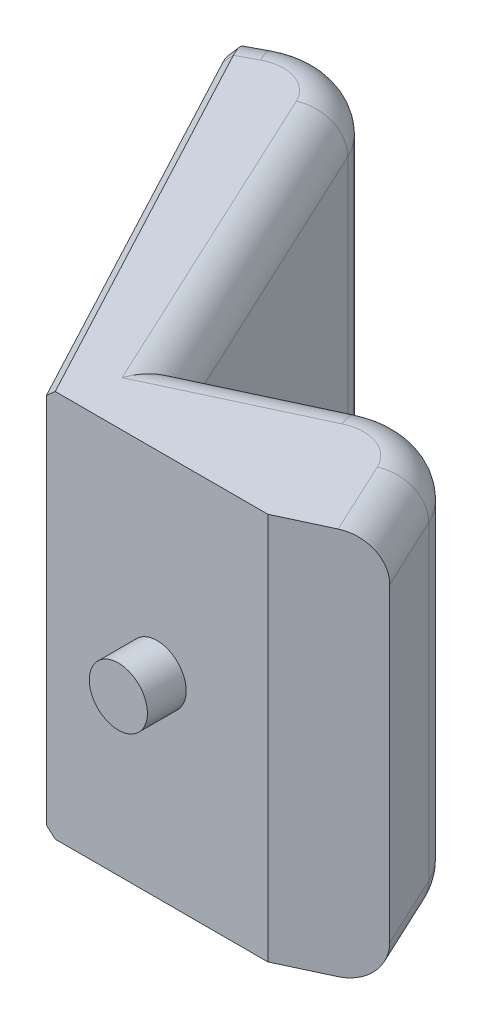
SolidWorks part; units mm, degrees
ref_plane "Front Plane" through (0, 0, 0) normal (0, 0, 1) x (1, 0, 0)
ref_plane "Top Plane" through (0, 0, 0) normal (0, 1, 0) x (1, 0, 0)
ref_plane "Right Plane" through (0, 0, 0) normal (1, 0, 0) x (0, 0, -1)
sketch "Sketch1" plane through (0, 0, 0) normal (0, 1, 0) x (1, 0, 0)
  line L0 (-56.3196, 105.9628) -> (0, 0)
  line L1 (0, 0) -> (57.1, 0)
  line L2 (57.1, 0) -> (78.5451, 10)
  line L3 (78.5451, 10) -> (69.7457, 28.8703)
  line L4 (42.3294, 38.849) -> (12.6301, 25)
  line L5 (12.6301, 25) -> (-22.4141, 100.1524)
  line L6 (-49.9268, 109.3605) -> (-56.3196, 105.9628)
  arc A0 (69.7457, 28.8703) -> (42.3294, 38.849) centre (51.0482, 20.1515) ccw
  arc A1 (-22.4141, 100.1524) -> (-49.9268, 109.3605) centre (-40.5402, 91.7001) ccw
  point P12 (-31.3196, 119.2503)
  dimension "D1" = 120
  dimension "D8" = 20
  dimension "D2" = 57.1
  dimension "D3" = 10
  dimension "D4" = 25
  dimension "D5" = 53.4
  dimension "D6" = 25
  dimension "D7" = 25
extrude "Boss-Extrude1" add sketch "Sketch1" along normal mid plane 100
sketch "Sketch2" plane through (0, 0, 0) normal (0, 0, 1) x (1, 0, 0)
  line L0 (0, 0) -> (57.1, 0) construction
  line L1 (57.1, 50) -> (57.1, -50) construction
  circle A0 centre (28.55, 0) radius 7.5
  dimension "D1" = 15
extrude "Boss-Extrude2" add sketch "Sketch2" along normal blind 10
fillet "Fillet1" radius 10 12 edges at (-53.1232, -50, -107.6616) (-34.1926, -50, -110.666) (74.1454, -50, -19.4351) (27.4797, -50, -31.9245) (74.1454, 50, -19.4351) (27.4797, 50, -31.9245) (-53.1232, 50, -107.6616) (-34.1926, 50, -110.666) (-4.892, -50, -62.5762) (58.1042, -50, -39.5378) (58.1042, 50, -39.5378) (-4.892, 50, -62.5762)
chamfer "Chamfer1" distance 2 angle 45 5 edges at (-25.8131, 50, -48.5663) (-54.9449, 47.0711, -103.3764) (-56.3196, 0, -105.9628) (-25.8131, -50, -48.5663) (-54.9449, -47.0711, -103.3764)
